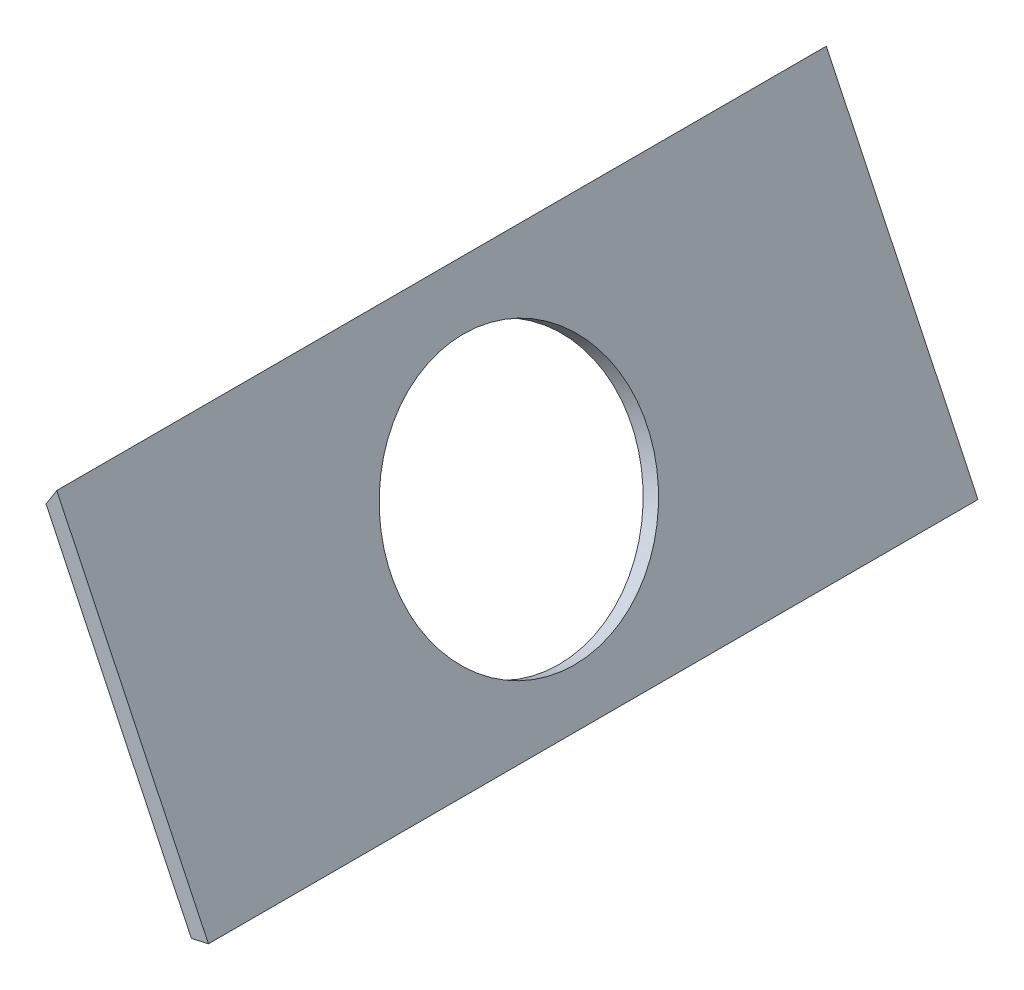
SolidWorks part; units mm, degrees
ref_plane "Ebene vorne" through (0, 0, 0) normal (0, 0, 1) x (1, 0, 0)
ref_plane "Ebene oben" through (0, 0, 0) normal (0, 1, 0) x (1, 0, 0)
ref_plane "Ebene rechts" through (0, 0, 0) normal (1, 0, 0) x (0, 0, -1)
sketch "Skizze1" plane through (0, 0, 0) normal (0, 0, 1) x (1, 0, 0)
  line L0 (253.157, 264.0237) -> (246.8583, 254.0237)
  line L1 (341.8583, 78.7946) -> (331.8583, 76.5237)
  line L32 (341.8583, 78.7946) -> (253.157, 264.0237)
  line L33 (331.8583, 76.5237) -> (246.8583, 254.0237)
extrude "Aufsatz-Linear austragen1" add sketch "Skizze1" along normal blind 450
sketch "Skizze2" plane through (299.7621, 143.548, 0) normal (-0.9019, -0.4319, 0) x (0, 0, 1)
  line L0 (-47.258, 24.0869) -> (475.8298, 24.0869) construction
  line L1 (450, -74.3131) -> (0, -74.3131) construction
  line L2 (225, 204.6913) -> (225, -140.1434) construction
  line L3 (0, 122.4895) -> (0, -74.3131) construction
  point P9 (225, 24.0869)
  dimension "D1" = 98.4
  dimension "D2" = 225
hole_wizard "Ø15.0 (15) Durchmesser Bohrung1" positions "Skizze4" profile "Skizze5" hole size "Ø15.0" standard "DIN" end condition through all
sketch "Skizze4" plane through (299.7621, 143.548, 0) normal (-0.9019, -0.4319, 0) x (0, 0, 1)
  point P0 (225, 24.0869)
sketch "Skizze5" plane through (289.3588, 165.2725, 225) normal (0, 0, 1) x (0.4319, -0.9019, 0)
  line L0 (0, 0) -> (0, 90.0014)
  line L1 (0, 90.0014) -> (75, 90.0014)
  line L2 (75, 90.0014) -> (75, 0)
  line L5 (75, 0) -> (0, 0)
  line L11 (0, -6.35) -> (0, 107.95) construction
  dimension "Bohrerdurchmesser" = 150
  dimension "Bohrungstiefe" = 90.0014
